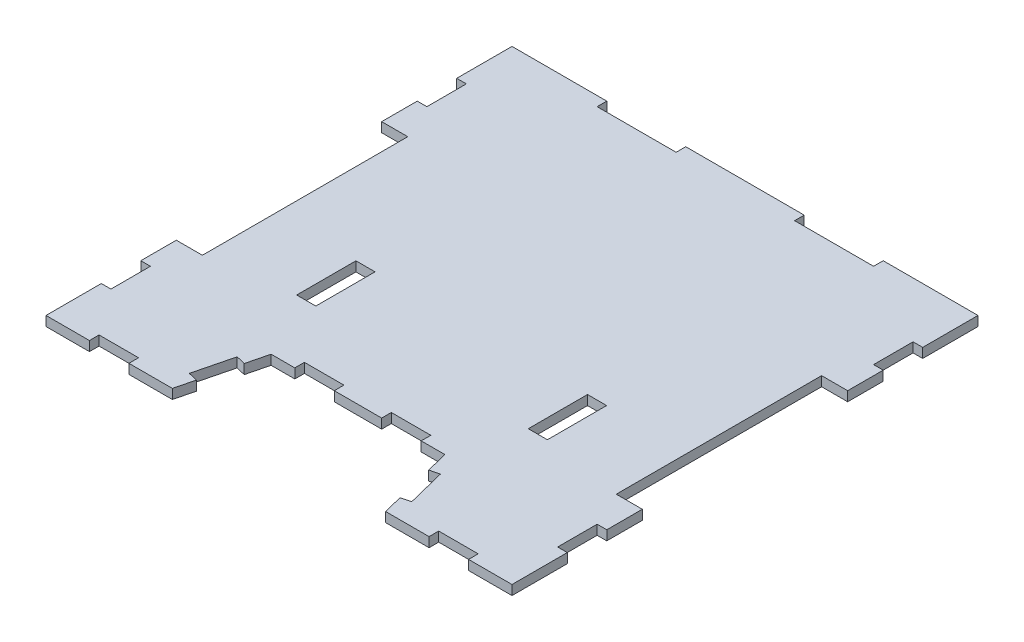
SolidWorks part; units mm, degrees
ref_plane "Alzado" through (0, 0, 0) normal (0, 0, 1) x (1, 0, 0)
ref_plane "Planta" through (0, 0, 0) normal (0, 1, 0) x (1, 0, 0)
ref_plane "Vista lateral" through (0, 0, 0) normal (1, 0, 0) x (0, 0, -1)
sketch "Croquis1" plane through (0, 0, 0) normal (0, 1, 0) x (1, 0, 0)
  line L0 (-59, 45) -> (-59, 59)
  line L1 (-59, -59) -> (-48, -59)
  line L2 (-59, -59) -> (-59, -45)
  line L3 (-59, 59) -> (-35, 59)
  line L4 (59, -59) -> (59, -45)
  line L5 (-59, -59) -> (59, 59) construction
  line L6 (-59, 59) -> (59, -59) construction
  line L7 (-59, 45) -> (-56.56, 45)
  line L8 (0, 0) -> (20.107, 0) construction
  line L9 (-59, 35) -> (-56.56, 35)
  line L10 (-56.56, 45) -> (-56.56, 35)
  line L11 (0, 0) -> (0, 20.2518) construction
  line L12 (-59, -35) -> (-56.56, -35)
  line L13 (-56.56, -45) -> (-56.56, -35)
  line L14 (-59, -45) -> (-56.56, -45)
  line L15 (59, 45) -> (56.56, 45)
  line L16 (59, 35) -> (56.56, 35)
  line L17 (56.56, 45) -> (56.56, 35)
  line L18 (59, -45) -> (56.56, -45)
  line L19 (59, -35) -> (56.56, -35)
  line L20 (56.56, -45) -> (56.56, -35)
  line L21 (-59, -35) -> (-59, -26)
  line L22 (59, -35) -> (59, -26)
  line L23 (59, 45) -> (59, 59)
  line L24 (-15, 59) -> (15, 59)
  line L25 (35, 56.56) -> (15, 56.56)
  line L26 (-35, 59) -> (-35, 56.56)
  line L27 (-35, 56.56) -> (-15, 56.56)
  line L28 (-15, 59) -> (-15, 56.56)
  line L29 (15, 59) -> (15, 56.56)
  line L30 (35, 59) -> (35, 56.56)
  line L31 (35, 59) -> (59, 59)
  line L32 (59, 26) -> (59, 35)
  line L33 (52.4, -26) -> (59, -26)
  line L34 (52.4, -26) -> (52.4, 26)
  line L35 (52.4, 26) -> (59, 26)
  line L36 (-52.4, 26) -> (-59, 26)
  line L37 (52.4, -26) -> (59, 26) construction
  line L38 (52.4, 26) -> (59, -26) construction
  line L39 (-52.4, -26) -> (-52.4, 26)
  line L40 (-52.4, -26) -> (-59, -26)
  line L41 (-59, 26) -> (-59, 35)
  line L42 (31.74, -22.78) -> (31.74, -7.78)
  line L43 (-31.74, -22.78) -> (-26.9, -22.78)
  line L44 (-31.74, -22.78) -> (-31.74, -7.78)
  line L45 (-31.74, -7.78) -> (-26.9, -7.78)
  line L46 (-26.9, -22.78) -> (-26.9, -7.78)
  line L47 (26.9, -22.78) -> (26.9, -7.78)
  line L48 (31.74, -7.78) -> (26.9, -7.78)
  line L49 (31.74, -22.78) -> (26.9, -22.78)
  line L50 (-22, -39) -> (-16, -39)
  line L51 (-22, -39) -> (-23.362, -44.4479)
  line L52 (22, -39) -> (23.362, -44.4479)
  line L53 (27, -59) -> (38, -59)
  line L54 (16, -39) -> (22, -39)
  line L55 (-6, -36.56) -> (-16, -36.56)
  line L56 (6, -39) -> (6, -36.56)
  line L57 (6, -36.56) -> (16, -36.56)
  line L58 (16, -39) -> (16, -36.56)
  line L59 (-6, -39) -> (-6, -36.56)
  line L60 (-16, -39) -> (-16, -36.56)
  line L61 (-6, -39) -> (6, -39)
  line L62 (-25.7873, -54.1493) -> (-28.1545, -53.5575)
  line L63 (25.7873, -54.1493) -> (28.1545, -53.5575)
  line L64 (23.362, -44.4479) -> (25.7291, -43.8561)
  line L65 (28.1545, -53.5575) -> (25.7291, -43.8561)
  line L66 (25.7873, -54.1493) -> (27, -59)
  line L67 (-28.1545, -53.5575) -> (-25.7291, -43.8561)
  line L68 (-23.362, -44.4479) -> (-25.7291, -43.8561)
  line L69 (-25.7873, -54.1493) -> (-27, -59)
  line L70 (48, -59) -> (59, -59)
  line L71 (-38, -59) -> (-38, -56.56)
  line L72 (38, -59) -> (38, -56.56)
  line L73 (38, -56.56) -> (48, -56.56)
  line L74 (48, -59) -> (48, -56.56)
  line L75 (-38, -56.56) -> (-48, -56.56)
  line L76 (-48, -59) -> (-48, -56.56)
  line L77 (-38, -59) -> (-27, -59)
  point P0 (0, 0)
  point P33 (55.7, 0)
  dimension "D1" = 118
  dimension "D2" = 118
  dimension "D3" = 35
  dimension "D4" = 10
  dimension "D5" = 2.44
  dimension "D6" = 15
  dimension "D7" = 20
  dimension "D8" = 2.44
  dimension "D9" = 52
  dimension "D10" = 6.6
  dimension "D11" = 36.22
  dimension "D12" = 27.26
  dimension "D13" = 4.84
  dimension "D14" = 15
  dimension "D15" = 11
  dimension "D16" = 44
  dimension "D17" = 54
  dimension "D18" = 27
  dimension "D19" = 20
  dimension "D20" = 6
  dimension "D21" = 10
  dimension "D22" = 2.44
  dimension "D23" = 5
  dimension "D24" = 10
  dimension "D25" = 2.44
  dimension "D26" = 10
  dimension "D27" = 2.44
extrude "Saliente-Extruir1" add sketch "Croquis1" along normal blind 2.44
